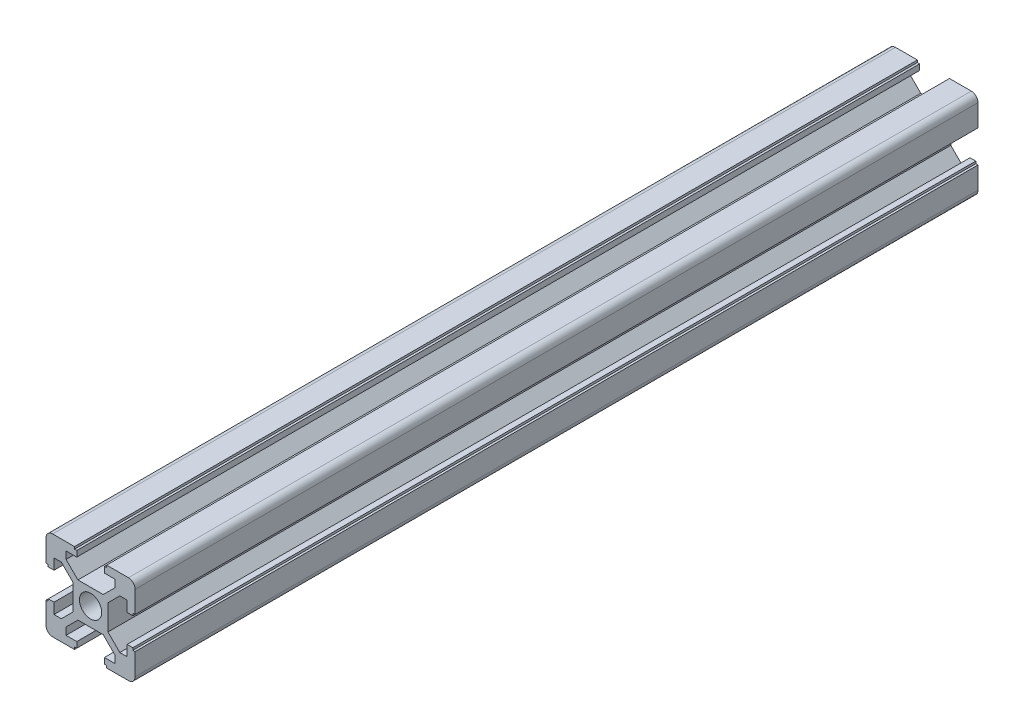
SolidWorks part; units mm, degrees
ref_plane "Front Plane" through (0, 0, 0) normal (0, 0, 1) x (1, 0, 0)
ref_plane "Top Plane" through (0, 0, 0) normal (0, 1, 0) x (1, 0, 0)
ref_plane "Right Plane" through (0, 0, 0) normal (1, 0, 0) x (0, 0, -1)
sketch "Sketch1" plane through (0, 0, 0) normal (0, 0, 1) x (1, 0, 0)
  line L0 (0, 13.3843) -> (0, -12.9126) construction
  line L1 (-14.4653, 0) -> (14.4653, 0) construction
  line L2 (2.8393, 3.9) -> (5.5, 6.5607)
  line L3 (-8.5, 10) -> (-3.6, 10)
  line L4 (-10, 8.5) -> (-10, 3.6)
  line L5 (-8.5, -10) -> (-3.6, -10)
  line L6 (10, 8.5) -> (10, 3.6)
  line L7 (-10, 10) -> (10, -10) construction
  line L8 (-10, -10) -> (10, 10) construction
  line L9 (-5.5, 8.2) -> (-3.1, 8.2)
  line L10 (-5.9626, 4.902) -> (-4.902, 5.9626) construction
  line L11 (-2.8393, 3.9) -> (-5.5, 6.5607)
  line L12 (-5.5, 8.2) -> (-5.5, 6.5607)
  line L13 (-2.8393, 3.9) -> (2.8393, 3.9)
  line L14 (5.5, 8.2) -> (5.5, 6.5607)
  line L15 (-3.1, 9.5) -> (-3.1, 8.2)
  line L16 (3.1, 9.5) -> (3.1, 8.2)
  line L17 (-3.1, 9.5) -> (3.1, 9.5) construction
  line L18 (-3.1, 9.5) -> (-3.6, 9.5)
  line L19 (-3.6, 9.5) -> (-3.6, 10)
  line L20 (3.1, 9.5) -> (3.6, 9.5)
  line L21 (3.6, 9.5) -> (3.6, 10)
  line L22 (3.6, 10) -> (8.5, 10)
  line L23 (3.1, 8.2) -> (5.5, 8.2)
  line L24 (-9.5, -3.1) -> (-9.5, -3.6)
  line L25 (-9.5, -3.6) -> (-10, -3.6)
  line L26 (-9.5, -3.1) -> (-8.2, -3.1)
  line L27 (-8.2, -3.1) -> (-8.2, -5.5)
  line L28 (-8.2, -5.5) -> (-6.5607, -5.5)
  line L29 (-3.9, -2.8393) -> (-6.5607, -5.5)
  line L30 (-3.9, 2.8393) -> (-3.9, -2.8393)
  line L31 (-3.9, 2.8393) -> (-6.5607, 5.5)
  line L32 (-8.2, 5.5) -> (-6.5607, 5.5)
  line L33 (-8.2, 5.5) -> (-8.2, 3.1)
  line L34 (-9.5, 3.1) -> (-8.2, 3.1)
  line L35 (-9.5, 3.1) -> (-9.5, 3.6)
  line L36 (-9.5, 3.6) -> (-10, 3.6)
  line L37 (-3.6, -9.5) -> (-3.6, -10)
  line L38 (-3.1, -9.5) -> (-3.6, -9.5)
  line L39 (-3.1, -9.5) -> (-3.1, -8.2)
  line L40 (-3.1, -8.2) -> (-5.5, -8.2)
  line L41 (-5.5, -8.2) -> (-5.5, -6.5607)
  line L42 (-2.8393, -3.9) -> (-5.5, -6.5607)
  line L43 (2.8393, -3.9) -> (-2.8393, -3.9)
  line L44 (2.8393, -3.9) -> (5.5, -6.5607)
  line L45 (5.5, -8.2) -> (5.5, -6.5607)
  line L46 (5.5, -8.2) -> (3.1, -8.2)
  line L47 (3.1, -9.5) -> (3.6, -9.5)
  line L48 (3.1, -9.5) -> (3.1, -8.2)
  line L49 (3.6, -9.5) -> (3.6, -10)
  line L50 (9.5, -3.6) -> (10, -3.6)
  line L51 (9.5, -3.1) -> (9.5, -3.6)
  line L52 (9.5, -3.1) -> (8.2, -3.1)
  line L53 (8.2, -5.5) -> (8.2, -3.1)
  line L54 (8.2, -5.5) -> (6.5607, -5.5)
  line L55 (3.9, -2.8393) -> (6.5607, -5.5)
  line L56 (3.9, -2.8393) -> (3.9, 2.8393)
  line L57 (3.9, 2.8393) -> (6.5607, 5.5)
  line L58 (8.2, 5.5) -> (6.5607, 5.5)
  line L59 (8.2, 3.1) -> (8.2, 5.5)
  line L60 (9.5, 3.1) -> (8.2, 3.1)
  line L61 (9.5, 3.1) -> (9.5, 3.6)
  line L62 (9.5, 3.6) -> (10, 3.6)
  line L63 (-10, -3.6) -> (-10, -8.5)
  line L64 (3.6, -10) -> (8.5, -10)
  line L65 (10, -3.6) -> (10, -8.5)
  arc A0 (8.5, 10) -> (10, 8.5) centre (8.5, 8.5) cw
  arc A1 (8.5, -10) -> (10, -8.5) centre (8.5, -8.5) ccw
  arc A2 (-10, -8.5) -> (-8.5, -10) centre (-8.5, -8.5) ccw
  arc A3 (-8.5, 10) -> (-10, 8.5) centre (-8.5, 8.5) ccw
  circle A4 centre (0, 0.2358) radius 2.5
  point P5 (0, 0)
  point P30 (-5.4323, 5.4323)
  point P38 (0, 9.5)
  dimension "D3" = 1.5
  dimension "D15" = 5
  dimension "D1" = 20
  dimension "D2" = 20
  dimension "D4" = 6.2
  dimension "D5" = 11
  dimension "D6" = 1.8
  dimension "D7" = 1.5
  dimension "D8" = 90
  dimension "D9" = 0.5
  dimension "D10" = 0.5
  dimension "D11" = 0.5
  dimension "D12" = 0.5
  dimension "D13" = 6.1
  dimension "D14" = 45
extrude "Boss-Extrude1" add sketch "Sketch1" along normal blind 189.0961
scale "缩放比例1" bodies to scale 101 scale about centroid uniform scaling yes scale factor 1
scale "缩放比例2" scale about centroid uniform scaling yes scale factor 3
scale "缩放比例3" scale about centroid uniform scaling yes scale factor 6
scale "缩放比例5" scale about centroid uniform scaling yes scale factor 2
scale "缩放比例6" scale about centroid uniform scaling yes scale factor 0.25
scale "缩放比例7" scale about centroid uniform scaling yes scale factor 0.125
scale "缩放比例8" scale about centroid uniform scaling yes scale factor 0.25
scale "缩放比例9" scale about centroid uniform scaling yes scale factor 4
scale "缩放比例10" scale about centroid uniform scaling yes scale factor 4
